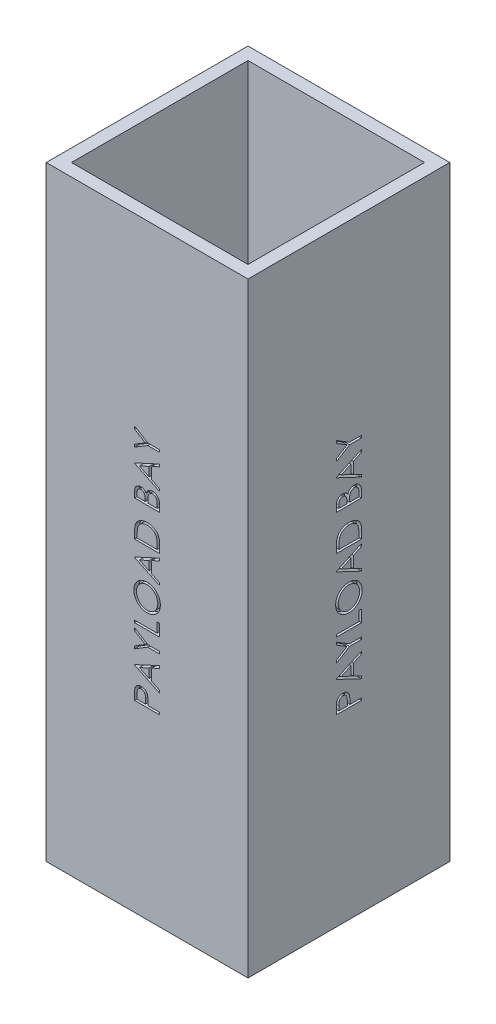
SolidWorks part; units mm, degrees
material "PVC Rigid"
ref_plane "Front Plane" through (0, 0, 0) normal (0, 0, 1) x (1, 0, 0)
ref_plane "Top Plane" through (0, 0, 0) normal (0, 1, 0) x (1, 0, 0)
ref_plane "Right Plane" through (0, 0, 0) normal (1, 0, 0) x (0, 0, -1)
sketch "Sketch1" plane through (0, 0, 0) normal (0, 1, 0) x (1, 0, 0)
  line L1 (-50.8, -50.8) -> (50.8, -50.8)
  line L2 (-50.8, -50.8) -> (-50.8, 50.8)
  line L3 (-50.8, 50.8) -> (50.8, 50.8)
  line L4 (50.8, -50.8) -> (50.8, 50.8)
  line L5 (-50.8, -50.8) -> (50.8, 50.8) construction
  line L6 (-50.8, 50.8) -> (50.8, -50.8) construction
  line L7 (-44.45, -44.45) -> (44.45, -44.45)
  line L8 (-44.45, -44.45) -> (-44.45, 44.45)
  line L9 (-44.45, 44.45) -> (44.45, 44.45)
  line L10 (44.45, -44.45) -> (44.45, 44.45)
  line L11 (-44.45, -44.45) -> (44.45, 44.45) construction
  line L12 (-44.45, 44.45) -> (44.45, -44.45) construction
  point P0 (0, 0)
  point P6 (0, 0)
  dimension "D1" = 101.6
  dimension "D2" = 101.6
  dimension "D3" = 88.9
extrude "Boss-Extrude1" add sketch "Sketch1" along normal blind 304.8
sketch "Sketch6" plane through (-50.8, 0, 0) normal (-1, 0, 0) x (0, 0, 1)
  line L0 (6.35, 0) -> (6.35, 304.8) construction
  line L1 (-50.8, 0) -> (50.8, 0) construction
  line L2 (-50.8, 304.8) -> (50.8, 304.8) construction
  line L3 (-50.8, 304.8) -> (-50.8, 0) construction
  text T0 "PAYLOAD BAY" font "Century Gothic" height in points 48
  dimension "D1" = 57.15
extrude "Cut-Extrude1" cut sketch "Sketch6" against normal blind 2.54
sketch "Sketch7" plane through (0, 0, 0) normal (0, 0, 1) x (1, 0, 0)
  line L0 (0, 0) -> (0, 304.8) construction
  line L1 (-50.8, 304.8) -> (50.8, 304.8) construction
pattern_circular "CirPattern1" count 4 over 360 about axis through (0, 0, 0) along (0, 1, 0) of "Cut-Extrude1"
